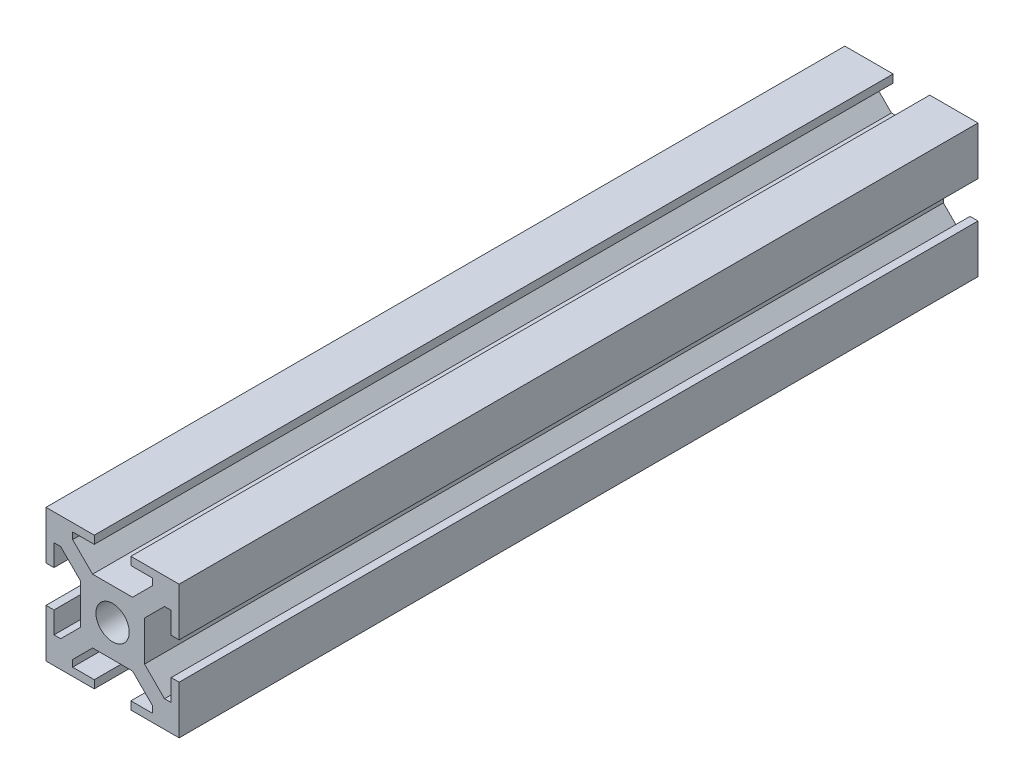
SolidWorks part; units mm, degrees
ref_plane "Plan de face" through (0, 0, 0) normal (0, 0, 1) x (1, 0, 0)
ref_plane "Plan de dessus" through (0, 0, 0) normal (0, 1, 0) x (1, 0, 0)
ref_plane "Plan de droite" through (0, 0, 0) normal (1, 0, 0) x (0, 0, -1)
sketch "Esquisse1" plane through (0, 0, 0) normal (0, 0, 1) x (1, 0, 0)
  line L1 (-22.5051, 0.0904) -> (-2.5051, 0.0904)
  line L2 (-22.5051, 0.0904) -> (-22.5051, -19.9096)
  line L3 (-22.5051, -19.9096) -> (-2.5051, -19.9096)
  line L4 (-2.5051, 0.0904) -> (-2.5051, -19.9096)
  dimension "D1" = 20
  dimension "D2" = 20
extrude "Boss.-Extru.1" add sketch "Esquisse1" along normal blind 120
sketch "Esquisse2" plane through (0, 0, 120) normal (0, 0, 1) x (1, 0, 0)
  line L0 (-22.5051, 0.0904) -> (-22.5051, -19.9096) construction
  line L1 (-22.5051, -7.1596) -> (-21.3051, -7.1596)
  line L2 (-22.5051, -7.1596) -> (-22.5051, -12.6596)
  line L3 (-22.5051, -12.6596) -> (-21.3051, -12.6596)
  line L4 (-21.3051, -7.1596) -> (-21.3051, -12.6596)
  line L5 (-2.5051, 0.0904) -> (-22.5051, 0.0904) construction
  line L6 (-15.2551, 0.0904) -> (-9.7551, 0.0904)
  line L7 (-15.2551, 0.0904) -> (-15.2551, -1.1096)
  line L8 (-15.2551, -1.1096) -> (-9.7551, -1.1096)
  line L9 (-9.7551, 0.0904) -> (-9.7551, -1.1096)
  line L10 (-2.5051, -19.9096) -> (-2.5051, 0.0904) construction
  line L11 (-2.5051, -7.1596) -> (-3.7051, -7.1596)
  line L12 (-2.5051, -7.1596) -> (-2.5051, -12.6596)
  line L13 (-2.5051, -12.6596) -> (-3.7051, -12.6596)
  line L14 (-3.7051, -7.1596) -> (-3.7051, -12.6596)
  line L15 (-22.5051, -19.9096) -> (-2.5051, -19.9096) construction
  line L16 (-15.2551, -19.9096) -> (-9.7551, -19.9096)
  line L17 (-15.2551, -19.9096) -> (-15.2551, -18.7096)
  line L18 (-15.2551, -18.7096) -> (-9.7551, -18.7096)
  line L19 (-9.7551, -19.9096) -> (-9.7551, -18.7096)
  dimension "D1" = 1.2
  dimension "D2" = 1.2
  dimension "D3" = 1.2
  dimension "D4" = 1.2
  dimension "D5" = 5.5
  dimension "D6" = 5.5
  dimension "D7" = 5.5
  dimension "D8" = 5.5
  dimension "D9" = 7.25
  dimension "D10" = 7.25
  dimension "D11" = 7.25
  dimension "D12" = 7.25
extrude "Enlèv. mat.-Extru.1" cut sketch "Esquisse2" against normal through all
sketch "Esquisse3" plane through (0, 0, 120) normal (0, 0, 1) x (1, 0, 0)
  line L0 (-15.2551, 0.0904) -> (-22.5051, 0.0904) construction
  line L1 (-21.3051, -15.9096) -> (-20.3051, -15.9096)
  line L2 (-21.3051, -15.9096) -> (-21.3051, -3.9096)
  line L3 (-21.3051, -3.9096) -> (-20.3051, -3.9096)
  line L4 (-17.3051, -12.9096) -> (-17.3051, -6.9096)
  line L5 (-18.5051, -1.1096) -> (-6.5051, -1.1096)
  line L6 (-18.5051, -1.1096) -> (-18.5051, -2.1096)
  line L7 (-15.5051, -5.1096) -> (-9.5051, -5.1096)
  line L8 (-6.5051, -1.1096) -> (-6.5051, -2.1096)
  line L9 (-3.7051, -3.9096) -> (-4.7051, -3.9096)
  line L10 (-3.7051, -3.9096) -> (-3.7051, -15.9096)
  line L11 (-3.7051, -15.9096) -> (-4.7051, -15.9096)
  line L12 (-7.7051, -6.9096) -> (-7.7051, -12.9096)
  line L13 (-6.5051, -18.7096) -> (-18.5051, -18.7096)
  line L14 (-6.5051, -18.7096) -> (-6.5051, -17.7096)
  line L15 (-9.5051, -14.7096) -> (-15.5051, -14.7096)
  line L16 (-18.5051, -18.7096) -> (-18.5051, -17.7096)
  line L17 (-2.5051, -7.1596) -> (-2.5051, 0.0904) construction
  line L18 (-15.2551, -1.1096) -> (-9.7551, -1.1096) construction
  line L19 (-3.7051, -7.1596) -> (-3.7051, -12.6596) construction
  line L20 (-9.7551, -19.9096) -> (-2.5051, -19.9096) construction
  line L21 (-22.5051, -12.6596) -> (-22.5051, -19.9096) construction
  line L22 (-22.5051, -19.9096) -> (-15.2551, -19.9096) construction
  line L23 (-15.5051, -14.7096) -> (-18.5051, -17.7096)
  line L24 (-20.3051, -15.9096) -> (-17.3051, -12.9096)
  line L25 (-6.5051, -17.7096) -> (-9.5051, -14.7096)
  line L26 (-4.7051, -15.9096) -> (-7.7051, -12.9096)
  line L27 (-4.7051, -3.9096) -> (-7.7051, -6.9096)
  line L28 (-9.5051, -5.1096) -> (-6.5051, -2.1096)
  line L29 (-18.5051, -2.1096) -> (-15.5051, -5.1096)
  line L30 (-20.3051, -3.9096) -> (-17.3051, -6.9096)
  point P1 (-17.3051, -3.9096)
  point P3 (-17.3051, -15.9096)
  point P5 (-6.5051, -5.1096)
  point P6 (-18.5051, -5.1096)
  point P9 (-7.7051, -15.9096)
  point P11 (-7.7051, -3.9096)
  point P13 (-18.5051, -14.7096)
  point P14 (-6.5051, -14.7096)
  point P24 (-6.1301, -19.9096)
  dimension "D1" = 4
  dimension "D2" = 4
  dimension "D3" = 4
  dimension "D4" = 4
  dimension "D5" = 12
  dimension "D6" = 4
  dimension "D7" = 12
  dimension "D8" = 4
  dimension "D9" = 0
  dimension "D10" = 0
  dimension "D11" = 4
  dimension "D12" = 12
  dimension "D13" = 12
  dimension "D14" = 4
  dimension "D15" = 1.2
  dimension "D16" = 1.2
  dimension "D17" = 3
  dimension "D18" = 3
  dimension "D19" = 3
  dimension "D20" = 3
  dimension "D21" = 3
  dimension "D22" = 3
  dimension "D23" = 3
  dimension "D24" = 3
  dimension "D25" = 3
  dimension "D26" = 3
  dimension "D27" = 3
  dimension "D28" = 3
  dimension "D29" = 3
  dimension "D30" = 3
  dimension "D31" = 3
  dimension "D32" = 3
extrude "Enlèv. mat.-Extru.2" cut sketch "Esquisse3" against normal through all
sketch "Esquisse4" plane through (0, 0, 120) normal (0, 0, 1) x (1, 0, 0)
  line L0 (-15.5051, -5.1096) -> (-9.5051, -5.1096) construction
  line L2 (-17.3051, -12.9096) -> (-17.3051, -6.9096) construction
  circle A0 centre (-12.5051, -9.9096) radius 2.5
  dimension "D1" = 5
  dimension "D2" = 4.8
  dimension "D3" = 4.8
extrude "Enlèv. mat.-Extru.3" cut sketch "Esquisse4" against normal through all
